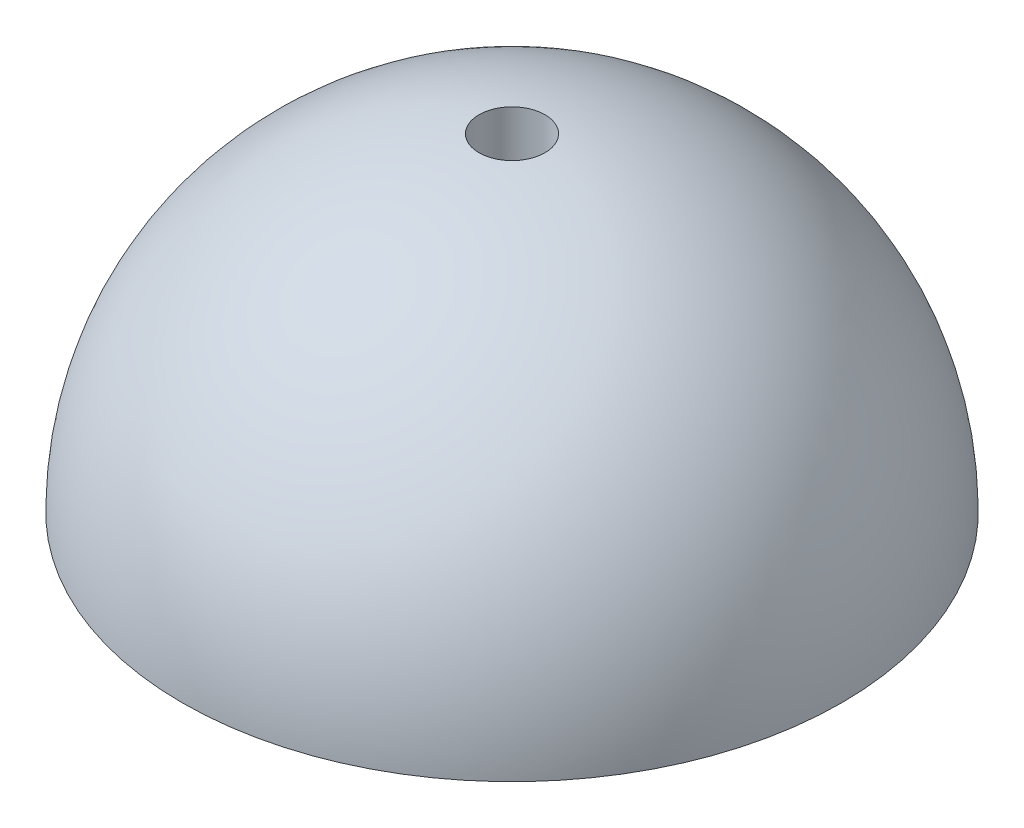
SolidWorks part; units mm, degrees
ref_plane "前视基准面" through (0, 0, 0) normal (0, 0, 1) x (1, 0, 0)
ref_plane "上视基准面" through (0, 0, 0) normal (0, 1, 0) x (1, 0, 0)
ref_plane "右视基准面" through (0, 0, 0) normal (1, 0, 0) x (0, 0, -1)
sketch "草图2" plane through (0, 0, 0) normal (0, 0, 1) x (1, 0, 0)
  line L0 (0, 0) -> (10, 0)
  line L1 (0, 10) -> (0, 0)
  arc A0 (10, 0) -> (0, 10) centre (0, 0) ccw
revolve "旋转1" add sketch "草图2" angle 360 about L1
sketch "草图3" plane through (0, 0, 0) normal (0, -1, 0) x (1, 0, 0)
  circle A0 centre (0, 0) radius 1
extrude "切除-拉伸1" cut sketch "草图3" against normal up to next
